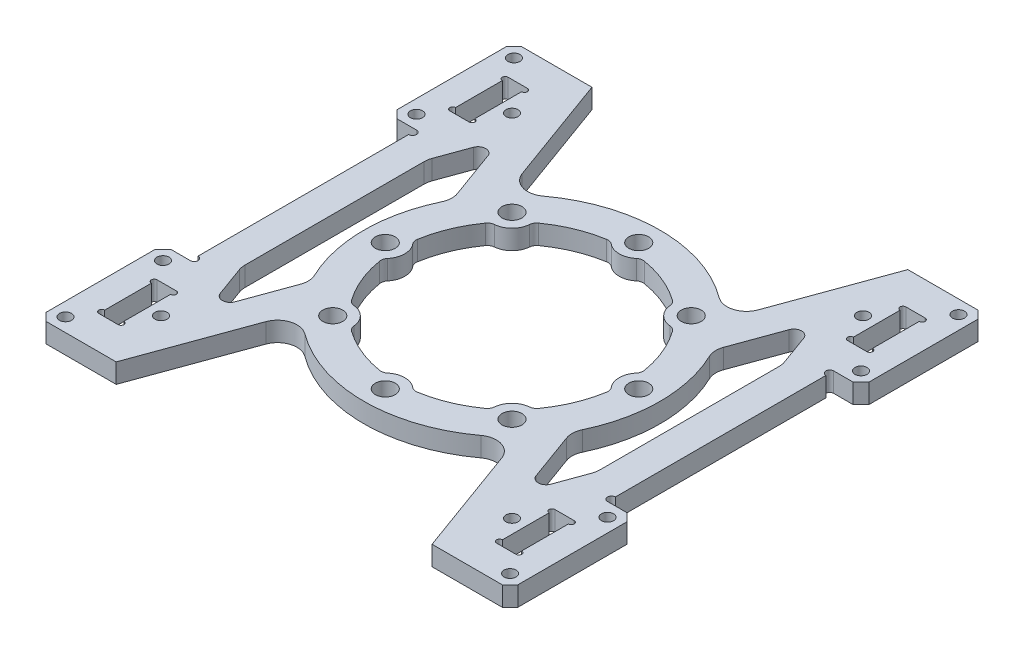
SolidWorks part; units mm, degrees
ref_plane "前视基准面" through (0, 0, 0) normal (0, 0, 1) x (1, 0, 0)
ref_plane "上视基准面" through (0, 0, 0) normal (0, 1, 0) x (1, 0, 0)
ref_plane "右视基准面" through (0, 0, 0) normal (1, 0, 0) x (0, 0, -1)
sketch "草图1" plane through (0, 0, 0) normal (0, 1, 0) x (1, 0, 0)
  line L0 (0, 45) -> (0, -45) construction
  line L1 (51, -45) -> (-51, -45) construction
  line L2 (51, -45) -> (51, 45) construction
  line L3 (51, 45) -> (-51, 45) construction
  line L4 (-51, -45) -> (-51, 45) construction
  line L5 (51, -45) -> (-51, 45) construction
  line L6 (51, 45) -> (-51, -45) construction
  line L7 (-53.475, 37.525) -> (-48.525, 37.525)
  line L8 (-53.475, 37.525) -> (-53.475, 52.475)
  line L9 (-53.475, 52.475) -> (-48.525, 52.475)
  line L10 (-48.525, 37.525) -> (-48.525, 52.475)
  line L11 (-53.475, 37.525) -> (-48.525, 52.475) construction
  line L12 (-53.475, 52.475) -> (-48.525, 37.525) construction
  line L13 (-53.475, -52.475) -> (-48.525, -52.475)
  line L14 (-53.475, -52.475) -> (-53.475, -37.525)
  line L15 (-53.475, -37.525) -> (-48.525, -37.525)
  line L16 (-48.525, -52.475) -> (-48.525, -37.525)
  line L17 (-53.475, -52.475) -> (-48.525, -37.525) construction
  line L18 (-53.475, -37.525) -> (-48.525, -52.475) construction
  line L19 (48.525, -52.475) -> (53.475, -52.475)
  line L20 (48.525, -52.475) -> (48.525, -37.525)
  line L21 (48.525, -37.525) -> (53.475, -37.525)
  line L22 (53.475, -52.475) -> (53.475, -37.525)
  line L23 (48.525, -52.475) -> (53.475, -37.525) construction
  line L24 (48.525, -37.525) -> (53.475, -52.475) construction
  line L25 (48.525, 37.525) -> (53.475, 37.525)
  line L26 (48.525, 37.525) -> (48.525, 52.475)
  line L27 (48.525, 52.475) -> (53.475, 52.475)
  line L28 (53.475, 37.525) -> (53.475, 52.475)
  line L29 (48.525, 37.525) -> (53.475, 52.475) construction
  line L30 (48.525, 52.475) -> (53.475, 37.525) construction
  line L31 (-51, 0) -> (51, 0) construction
  line L32 (-57, 57.5) -> (-57, 32.5) construction
  line L34 (60.5, -61) -> (-60.5, -61)
  line L35 (60.5, -61) -> (60.5, 61)
  line L36 (60.5, 61) -> (-60.5, 61)
  line L37 (-60.5, -61) -> (-60.5, 61)
  line L38 (60.5, -61) -> (-60.5, 61) construction
  line L39 (60.5, 61) -> (-60.5, -61) construction
  circle A0 centre (0, 0) radius 32.5 construction
  circle A1 centre (0, 32.5) radius 2.55
  circle A2 centre (22.981, 22.981) radius 2.55
  circle A3 centre (32.5, 0) radius 2.55
  circle A4 centre (22.981, -22.981) radius 2.55
  circle A5 centre (0, -32.5) radius 2.55
  circle A6 centre (-22.981, -22.981) radius 2.55
  circle A7 centre (-32.5, 0) radius 2.55
  circle A8 centre (-22.981, 22.981) radius 2.55
  arc A9 (-23.3747, 17.9965) -> (-29.2538, 3.803) centre (0, 0) ccw
  arc A10 (17.9965, 23.3747) -> (23.3747, 17.9965) centre (22.981, 22.981) ccw
  arc A11 (29.2538, 3.803) -> (29.2538, -3.803) centre (32.5, 0) ccw
  arc A12 (23.3747, -17.9965) -> (17.9965, -23.3747) centre (22.981, -22.981) ccw
  arc A13 (3.803, -29.2538) -> (-3.803, -29.2538) centre (0, -32.5) ccw
  arc A14 (-17.9965, -23.3747) -> (-23.3747, -17.9965) centre (-22.981, -22.981) ccw
  arc A15 (-29.2538, -3.803) -> (-29.2538, 3.803) centre (-32.5, 0) ccw
  arc A16 (-23.3747, 17.9965) -> (-17.9965, 23.3747) centre (-22.981, 22.981) ccw
  arc A17 (-3.803, 29.2538) -> (3.803, 29.2538) centre (0, 32.5) ccw
  arc A18 (-29.2538, -3.803) -> (-23.3747, -17.9965) centre (0, 0) ccw
  arc A19 (-17.9965, -23.3747) -> (-3.803, -29.2538) centre (0, 0) ccw
  arc A20 (3.803, -29.2538) -> (17.9965, -23.3747) centre (0, 0) ccw
  arc A21 (23.3747, -17.9965) -> (29.2538, -3.803) centre (0, 0) ccw
  arc A22 (29.2538, 3.803) -> (23.3747, 17.9965) centre (0, 0) ccw
  arc A23 (17.9965, 23.3747) -> (3.803, 29.2538) centre (0, 0) ccw
  arc A24 (-3.803, 29.2538) -> (-17.9965, 23.3747) centre (0, 0) ccw
  circle A25 centre (-57, 57.5) radius 1.55
  circle A26 centre (-57, 32.5) radius 1.55
  circle A27 centre (57, 32.5) radius 1.55
  circle A28 centre (57, 57.5) radius 1.55
  circle A29 centre (57, -32.5) radius 1.55
  circle A30 centre (57, -57.5) radius 1.55
  circle A31 centre (-57, -32.5) radius 1.55
  circle A32 centre (-57, -57.5) radius 1.55
  circle A33 centre (-45, 45) radius 1.55
  circle A34 centre (45, 45) radius 1.55
  circle A35 centre (45, -45) radius 1.55
  circle A36 centre (-45, -45) radius 1.55
  point P0 (0, 0)
  point P42 (0, 0)
  point P65 (-57, 45)
  dimension "D5" = 65
  dimension "D6" = 5.1
  dimension "D8" = 10
  dimension "D9" = 3
  dimension "D10" = 3.1
  dimension "D13" = 3.5
  dimension "D14" = 3.5
  dimension "D15" = 6
  dimension "D1" = 102
  dimension "D2" = 90
  dimension "D3" = 14.95
  dimension "D4" = 4.95
  dimension "D11" = 6
  dimension "D12" = 25
  dimension "D7" = 8
extrude "凸台-拉伸1" add sketch "草图1" along normal mid plane 5
fillet "圆角1" radius 2 16 edges at (-29.2538, 0, -3.803) (-29.2538, 0, 3.803) (-23.3747, 0, 17.9965) (-17.9965, 0, 23.3747) (-3.803, 0, 29.2538) (3.803, 0, 29.2538) (17.9965, 0, 23.3747) (23.3747, 0, 17.9965) (29.2538, 0, 3.803) (29.2538, 0, -3.803) (23.3747, 0, -17.9965) (17.9965, 0, -23.3747) (3.803, 0, -29.2538) (-3.803, 0, -29.2538) (-17.9965, 0, -23.3747) (-23.3747, 0, -17.9965)
sketch "草图2" plane through (0, 2.5, 0) normal (0, 1, 0) x (1, 0, 0)
  line L0 (-53.475, 52.475) -> (-53.475, 37.525) construction
  line L1 (-48.525, 37.525) -> (-48.525, 52.475) construction
  line L2 (-53.475, -37.525) -> (-53.475, -52.475) construction
  line L3 (-48.525, -52.475) -> (-48.525, -37.525) construction
  line L4 (48.525, -37.525) -> (48.525, -52.475) construction
  line L5 (53.475, -52.475) -> (53.475, -37.525) construction
  line L7 (48.525, 52.475) -> (48.525, 37.525) construction
  line L8 (53.475, 37.525) -> (53.475, 52.475) construction
  circle A0 centre (-53.475, 51.725) radius 0.75
  circle A1 centre (-53.475, 38.275) radius 0.75
  circle A2 centre (-48.525, 38.275) radius 0.75
  circle A3 centre (-48.525, 51.725) radius 0.75
  circle A4 centre (-53.475, -38.275) radius 0.75
  circle A5 centre (-48.525, -38.275) radius 0.75
  circle A6 centre (-53.475, -51.725) radius 0.75
  circle A7 centre (-48.525, -51.725) radius 0.75
  circle A8 centre (48.525, -51.725) radius 0.75
  circle A9 centre (53.475, -51.725) radius 0.75
  circle A10 centre (48.525, -38.275) radius 0.75
  circle A11 centre (53.475, -38.275) radius 0.75
  circle A12 centre (48.525, 51.725) radius 0.75
  circle A13 centre (53.475, 51.725) radius 0.75
  circle A14 centre (48.525, 38.275) radius 0.75
  circle A15 centre (53.475, 38.275) radius 0.75
  dimension "D1" = 1.5
extrude "切除-拉伸1" cut sketch "草图2" against normal through all
sketch "草图3" plane through (0, 2.5, 0) normal (0, 1, 0) x (1, 0, 0)
  line L0 (-60.5, 29) -> (-53.5, 29)
  line L1 (-60.5, 61) -> (-60.5, -61) construction
  line L2 (-53.5, 29) -> (-53.5, -29)
  line L3 (-53.5, -29) -> (-60.5, -29)
  line L4 (-60.5, -29) -> (-60.5, 29)
  line L5 (0, 32.5) -> (0, -32.5) construction
  line L6 (53.5, -29) -> (60.5, -29)
  line L7 (53.5, 29) -> (53.5, -29)
  line L8 (60.5, 29) -> (53.5, 29)
  line L9 (60.5, -29) -> (60.5, 29)
  circle A0 centre (-57, 32.5) radius 1.55 construction
  circle A1 centre (-57, -32.5) radius 1.55 construction
  dimension "D1" = 3.5
  dimension "D2" = 3.5
  dimension "D3" = 3.5
extrude "切除-拉伸2" cut sketch "草图3" against normal through all
sketch "草图4" plane through (0, 2.5, 0) normal (0, 1, 0) x (1, 0, 0)
  line L0 (-40.5, 61) -> (-27.7475, 25.9629)
  line L1 (40.5, 61) -> (27.7475, 25.9629)
  line L2 (-40.5, 61) -> (40.5, 61)
  line L3 (60.5, 61) -> (-60.5, 61) construction
  line L4 (-60.5, 61) -> (-60.5, 29) construction
  line L5 (-53.5, 0) -> (53.5, 0) construction
  line L6 (-53.5, -29) -> (-53.5, 29) construction
  line L7 (53.5, 29) -> (53.5, -29) construction
  line L8 (40.5, -61) -> (27.7475, -25.9629)
  line L9 (-40.5, -61) -> (40.5, -61)
  line L10 (-40.5, -61) -> (-27.7475, -25.9629)
  arc A0 (27.7475, 25.9629) -> (-27.7475, 25.9629) centre (0, 0) ccw
  arc A1 (27.7475, -25.9629) -> (-27.7475, -25.9629) centre (0, 0) cw
  dimension "D1" = 38
  dimension "D2" = 20
  dimension "D3" = 110
extrude "切除-拉伸3" cut sketch "草图4" against normal through all
fillet "圆角2" radius 5 4 edges at (-27.7475, 0, 25.9629) (27.7475, 0, 25.9629) (27.7475, 0, -25.9629) (-27.7475, 0, -25.9629)
sketch "草图5" plane through (0, 2.5, 0) normal (0, 1, 0) x (1, 0, 0)
  line L0 (-40.5, 37.6096) -> (-33.4045, 18.1147)
  line L1 (-40.5, 37.6096) -> (-45.5, 23.8722)
  line L2 (-45.5, 23.8722) -> (-45.5, -23.8722)
  line L3 (-45.5, -23.8722) -> (-40.5, -37.6096)
  line L4 (-40.5, -37.6096) -> (-33.4045, -18.1147)
  line L5 (-30.2605, -32.8671) -> (-40.5, -61) construction
  line L6 (-40.5, 61) -> (-30.2605, 32.8671) construction
  line L7 (-53.5, -29) -> (-53.5, 29) construction
  line L8 (0, 32.5) -> (0, -32.5) construction
  line L9 (40.5, 37.6096) -> (33.4045, 18.1147)
  line L10 (40.5, 37.6096) -> (45.5, 23.8722)
  line L11 (45.5, 23.8722) -> (45.5, -23.8722)
  line L12 (45.5, -23.8722) -> (40.5, -37.6096)
  line L13 (40.5, -37.6096) -> (33.4045, -18.1147)
  arc A0 (-33.4045, 18.1147) -> (-33.4045, -18.1147) centre (0, 0) ccw
  arc A1 (33.4045, 18.1147) -> (33.4045, -18.1147) centre (0, 0) cw
  point P5 (-45.5, 0)
  dimension "D1" = 76
  dimension "D2" = 8
  dimension "D3" = 8
extrude "切除-拉伸4" cut sketch "草图5" against normal through all
fillet "圆角3" radius 2 4 edges at (40.5, 0, 37.6096) (40.5, 0, -37.6096) (-40.5, 0, 37.6096) (-40.5, 0, -37.6096)
chamfer "倒角1" distance 2 angle 45 8 edges at (60.5, 0, -61) (60.5, 0, -29) (60.5, 0, 29) (60.5, 0, 61) (-60.5, 0, 61) (-60.5, 0, 29) (-60.5, 0, -29) (-60.5, 0, -61)
fillet "圆角4" radius 5 8 edges at (-33.4045, 0, 18.1147) (-45.5, 0, 23.8722) (-45.5, 0, -23.8722) (-33.4045, 0, -18.1147) (45.5, 0, 23.8722) (33.4045, 0, 18.1147) (33.4045, 0, -18.1147) (45.5, 0, -23.8722)
sketch "草图6" plane through (0, 2.5, 0) normal (0, 1, 0) x (1, 0, 0)
  line L0 (-53.5, -29) -> (-53.5, 29) construction
  line L1 (53.5, 29) -> (53.5, -29) construction
  circle A0 centre (-53.5, 28) radius 1
  circle A1 centre (-53.5, -28) radius 1
  circle A2 centre (53.5, -28) radius 1
  circle A3 centre (53.5, 28) radius 1
  dimension "D1" = 2
extrude "切除-拉伸5" cut sketch "草图6" against normal through all
